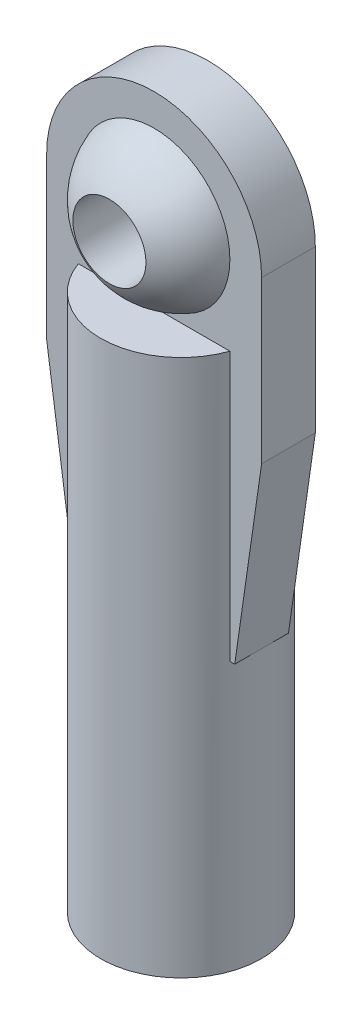
SolidWorks part; units mm, degrees
ref_plane "Front Plane" through (0, 0, 0) normal (0, 0, 1) x (1, 0, 0)
ref_plane "Top Plane" through (0, 0, 0) normal (0, 1, 0) x (1, 0, 0)
ref_plane "Right Plane" through (0, 0, 0) normal (1, 0, 0) x (0, 0, -1)
sketch "Sketch2" plane through (0, 0, 0) normal (0, 0, 1) x (1, 0, 0)
  line L0 (0, 6.0439) -> (0, -6.9998) construction
  line L1 (0, 2.3749) -> (0, -2.3749)
  arc A0 (0, -2.3749) -> (0, 2.3749) centre (0, 0) ccw
  dimension "D1" = 4.7498
revolve "Revolve1" add sketch "Sketch2" angle 360 about L0
sketch "Sketch3" plane through (0, 0, 0) normal (0, 0, 1) x (1, 0, 0)
  circle A0 centre (0, 0) radius 1.0795
  dimension "D1" = 2.159
extrude "Cut-Extrude1" cut sketch "Sketch3" against normal through all and the other way through all
sketch "Sketch4" plane through (0, 0, 0) normal (0, 0, 1) x (1, 0, 0)
  line L0 (-3.175, 0) -> (-3.175, -4.7625)
  line L1 (-3.175, -4.7625) -> (-2.3812, -10.287)
  line L2 (3.175, -4.7625) -> (2.3813, -10.287)
  line L3 (-2.3812, -10.287) -> (2.3813, -10.287)
  line L4 (0, -3.175) -> (0, -17.399) construction
  line L5 (3.175, 0) -> (3.175, -4.7625)
  arc A0 (3.175, 0) -> (-3.175, 0) centre (0, 0) ccw
  circle A1 centre (0, 0) radius 1.0795 construction
  circle A2 centre (0, 0) radius 1.0795
  point P9 (0, -10.287)
  dimension "D1" = 6.35
  dimension "D2" = 17.399
  dimension "D3" = 4.7625
  dimension "D4" = 4.7625
extrude "Boss-Extrude1" add sketch "Sketch4" along normal mid plane 1.5875
sketch "Sketch5" plane through (0, -10.287, 0) normal (0, -1, 0) x (1, 0, 0)
  circle A0 centre (0, 0) radius 2.3749
  arc A1 (2.2383, 0.7937) -> (1.0795, 2.1154) centre (0, 0) ccw construction
extrude "Boss-Extrude2" add sketch "Sketch5" against normal mid plane 15.875
hole_wizard "#4-40 Tapped Hole1" positions "Sketch7" profile "Sketch6" tap size "#4-40" standard "ANSI Inch"
sketch "Sketch7" plane through (0, -18.2245, 0) normal (0, -1, 0) x (-1, 0, 0)
  point P0 (0, 0)
sketch "Sketch6" plane through (0, -18.2245, 0) normal (1, 0, 0) x (0, 0, -1)
  line L0 (0, 0) -> (0, 13.3792)
  line L1 (0, 13.3792) -> (1.1303, 12.7)
  line L2 (1.1303, 12.7) -> (1.1303, 0)
  line L5 (1.1303, 0) -> (0, 0)
  line L10 (0, 13.3792) -> (-1.1303, 12.7) construction
  line L11 (0, -6.35) -> (0, 107.95) construction
  dimension "Tap Drill Dia." = 2.2606
  dimension "Tap Drill Depth" = 12.7
  dimension "Drill Angle" = 118
